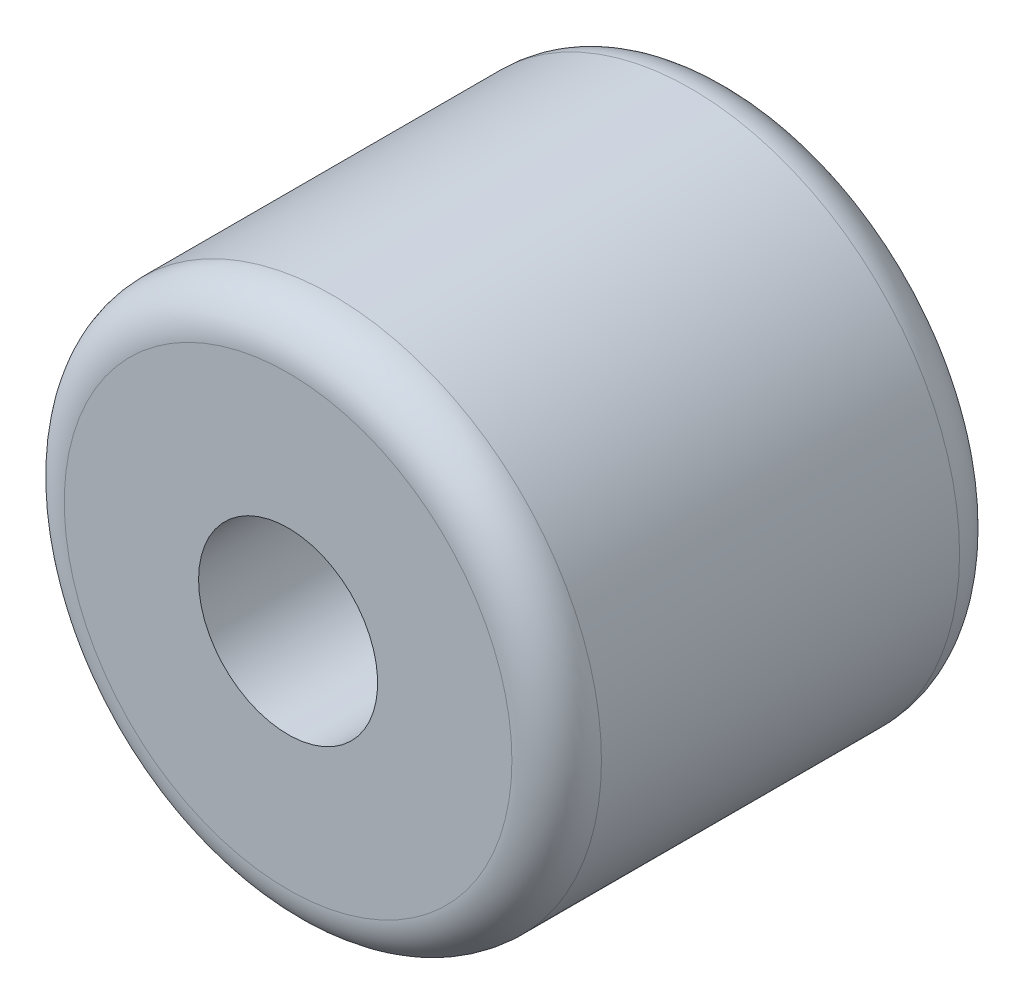
SolidWorks part; units mm, degrees
ref_plane "前视基准面" through (0, 0, 0) normal (0, 0, 1) x (1, 0, 0)
ref_plane "上视基准面" through (0, 0, 0) normal (0, 1, 0) x (1, 0, 0)
ref_plane "右视基准面" through (0, 0, 0) normal (1, 0, 0) x (0, 0, -1)
sketch "草图1" plane through (0, 0, 0) normal (0, 0, 1) x (1, 0, 0)
  circle A0 centre (0, 0) radius 6
  dimension "D1" = 12
extrude "凸台-拉伸1" add sketch "草图1" along normal blind 10
sketch "草图2" plane through (0, 0, 0) normal (0, 0, -1) x (-1, 0, 0)
  circle A0 centre (0, 0) radius 2
  dimension "D1" = 4
extrude "切除-拉伸1" cut sketch "草图2" against normal through all
fillet "圆角1" radius 1 2 edges at (6, 0, 0) (6, 0, 10)
